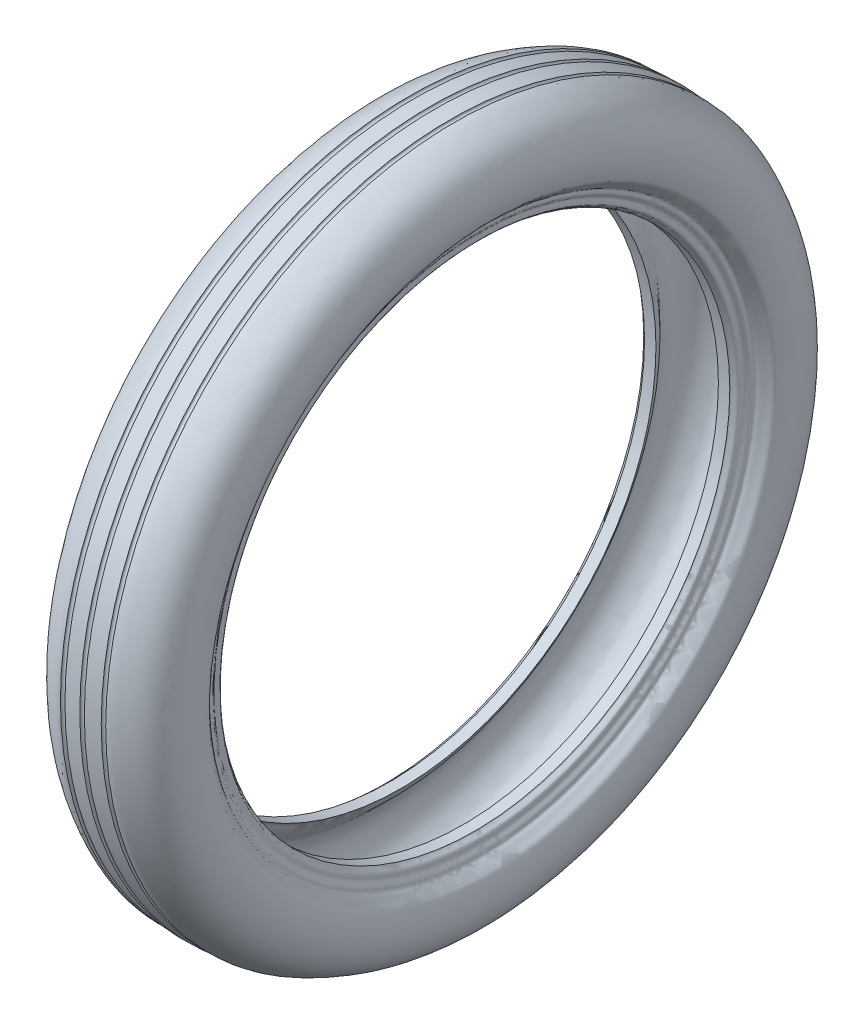
SolidWorks part; units mm, degrees
material "BUTYL"
ref_plane "Front Plane" through (0, 0, 0) normal (0, 0, 1) x (1, 0, 0)
ref_plane "Top Plane" through (0, 0, 0) normal (0, 1, 0) x (1, 0, 0)
ref_plane "Right Plane" through (0, 0, 0) normal (1, 0, 0) x (0, 0, -1)
sketch "Sketch1" plane through (0, 0, 0) normal (0, 0, 1) x (1, 0, 0)
  line L0 (51.6667, 341.5) -> (258.3333, 341.5) construction
  line L1 (43.3333, 103) -> (216.6667, 103) construction
  line L2 (0, 248.8346) -> (0, 0) construction
  line L3 (-24.8173, 203) -> (-33.9053, 203)
  line L4 (-14.4302, 277.4968) -> (-1.8191, 278.3033)
  line L5 (24.8173, 203) -> (33.9053, 203)
  line L6 (14.4302, 277.4968) -> (1.8191, 278.3033)
  line L7 (-102.7229, 0) -> (130.3407, 0) construction
  line L8 (-24.8173, 203) -> (24.8173, 203) construction
  arc A0 (-18.0013, 277.4968) -> (-14.4302, 277.4968) centre (-16.2157, 277.4968) ccw
  arc A1 (18.0013, 277.4968) -> (14.4302, 277.4968) centre (16.2157, 277.4968) cw
  arc A2 (-1.8191, 278.3033) -> (1.8191, 278.3033) centre (0, 278.3033) ccw
  spline S0 degree 3 poles (-24.8173, 203) (-27.2284, 205.0639) (-28.5496, 210.3276) (-33.6713, 215.0194) (-37.7773, 219.0104) (-42.2634, 223.062) (-45.1671, 229.5539) (-48.0287, 236.6578) (-47.888, 244.8825) (-46.3949, 254.0571) (-40.3487, 261.4036) (-33.8515, 268.8109) (-25.2444, 271.405) (-16.7423, 273.1864) (-10.1406, 273.4632) (-4.5443, 274.0141) (-1.7534, 273.4453) (0, 273.6518) knots 0 0 0 0 0.082233 0.137617 0.183009 0.237254 0.29747 0.371716 0.440605 0.515818 0.616104 0.690267 0.776014 0.84938 0.924773 0.95299 1 1 1 1
  spline S1 degree 3 poles (24.8173, 203) (27.2284, 205.0639) (28.5496, 210.3276) (33.6713, 215.0194) (37.7773, 219.0104) (42.2634, 223.062) (45.1671, 229.5539) (48.0287, 236.6578) (47.888, 244.8825) (46.3949, 254.0571) (40.3487, 261.4036) (33.8515, 268.8109) (25.2444, 271.405) (16.7423, 273.1864) (10.1406, 273.4632) (4.5443, 274.0141) (1.7534, 273.4453) (0, 273.6518) knots 0 0 0 0 0.082233 0.137617 0.183009 0.237254 0.29747 0.371716 0.440605 0.515818 0.616104 0.690267 0.776014 0.84938 0.924773 0.95299 1 1 1 1
  spline S2 degree 3 poles (-33.9053, 203) (-34.4514, 204.2233) (-38.4052, 205.2108) (-37.5895, 208.7025) (-37.3177, 211.6374) (-40.3679, 213.4652) (-39.0661, 217.0868) (-42.53, 218.9871) (-44.4812, 222.025) (-48.1613, 224.6642) (-49.3373, 231.2973) (-50.566, 239.2176) (-49.5419, 249.3098) (-46.4258, 258.7858) (-40.6849, 266.454) (-33.8688, 271.5447) (-26.5849, 275.2395) (-21.385, 277.7704) (-18.0013, 277.4968) knots 0 0 0 0 0.050285 0.080964 0.097206 0.139297 0.164562 0.195188 0.24242 0.280703 0.328072 0.440671 0.53315 0.638161 0.74644 0.823682 0.899585 1 1 1 1
  spline S3 degree 3 poles (33.9053, 203) (34.4514, 204.2233) (38.4052, 205.2108) (37.5895, 208.7025) (37.3177, 211.6374) (40.3679, 213.4652) (39.0661, 217.0868) (42.53, 218.9871) (44.4812, 222.025) (48.1613, 224.6642) (49.3373, 231.2973) (50.566, 239.2176) (49.5419, 249.3098) (46.4258, 258.7858) (40.6849, 266.454) (33.8688, 271.5447) (26.5849, 275.2395) (21.385, 277.7704) (18.0013, 277.4968) knots 0 0 0 0 0.050285 0.080964 0.097206 0.139297 0.164562 0.195188 0.24242 0.280703 0.328072 0.440671 0.53315 0.638161 0.74644 0.823682 0.899585 1 1 1 1
  dimension "D1" = 203
  dimension "D2" = 278.3033
revolve "Revolve2" add sketch "Sketch1" angle 360 about L7
move or copy body "Body-Move/Copy1" bodies to move or copy 102
